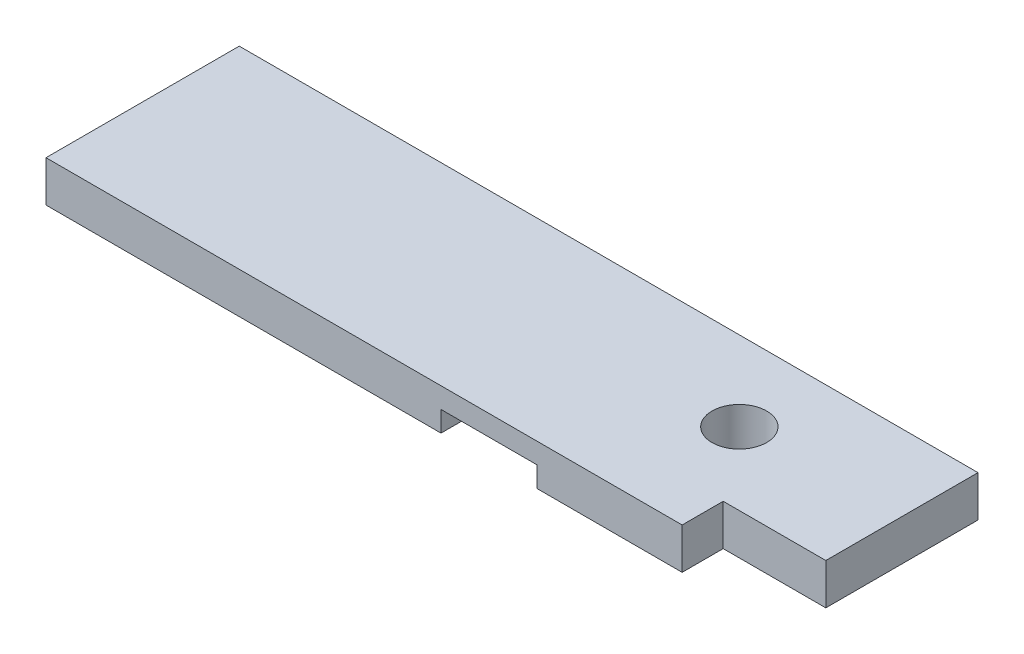
SolidWorks part; units mm, degrees
material "Pine"
ref_plane "Front Plane" through (0, 0, 0) normal (0, 0, 1) x (1, 0, 0)
ref_plane "Top Plane" through (0, 0, 0) normal (0, 1, 0) x (1, 0, 0)
ref_plane "Right Plane" through (0, 0, 0) normal (1, 0, 0) x (0, 0, -1)
sketch "Sketch1" plane through (0, 0, 0) normal (0, 1, 0) x (1, 0, 0)
  line L0 (685.8127, 0) -> (0, 0)
  line L5 (685.8127, 0) -> (685.8127, -141.2875)
  line L6 (590.5627, -179.4002) -> (0, -179.4002)
  line L8 (685.8127, -141.2875) -> (590.5627, -141.2875)
  line L9 (590.5627, -141.2875) -> (590.5627, -179.4002)
  line L10 (0, 0) -> (0, -179.4002)
  circle A0 centre (538.1752, -73.9182) radius 25.4
  dimension "D11" = 25.4
  dimension "D2" = 0
  dimension "D3" = 179.4002
  dimension "D4" = 590.5627
  dimension "D5" = 141.2875
  dimension "D6" = 538.1752
  dimension "D7" = 73.9182
  dimension "D8" = 685.8127
extrude "Boss-Extrude1" add sketch "Sketch1" along normal blind 38.1
sketch "Sketch2" plane through (0, 0, 0) normal (0, -1, 0) x (1, 0, 0)
  line L0 (0, 179.4002) -> (590.5627, 179.4002) construction
  line L1 (366.701, 179.4002) -> (455.601, 179.4002)
  line L2 (366.701, 179.4002) -> (366.701, 0)
  line L3 (366.701, 0) -> (455.601, 0)
  line L4 (455.601, 179.4002) -> (455.601, 0)
  line L5 (685.8127, 0) -> (0, 0) construction
  dimension "D1" = 88.9
  dimension "D2" = 366.701
extrude "Cut-Extrude1" cut sketch "Sketch2" against normal blind 19.05
